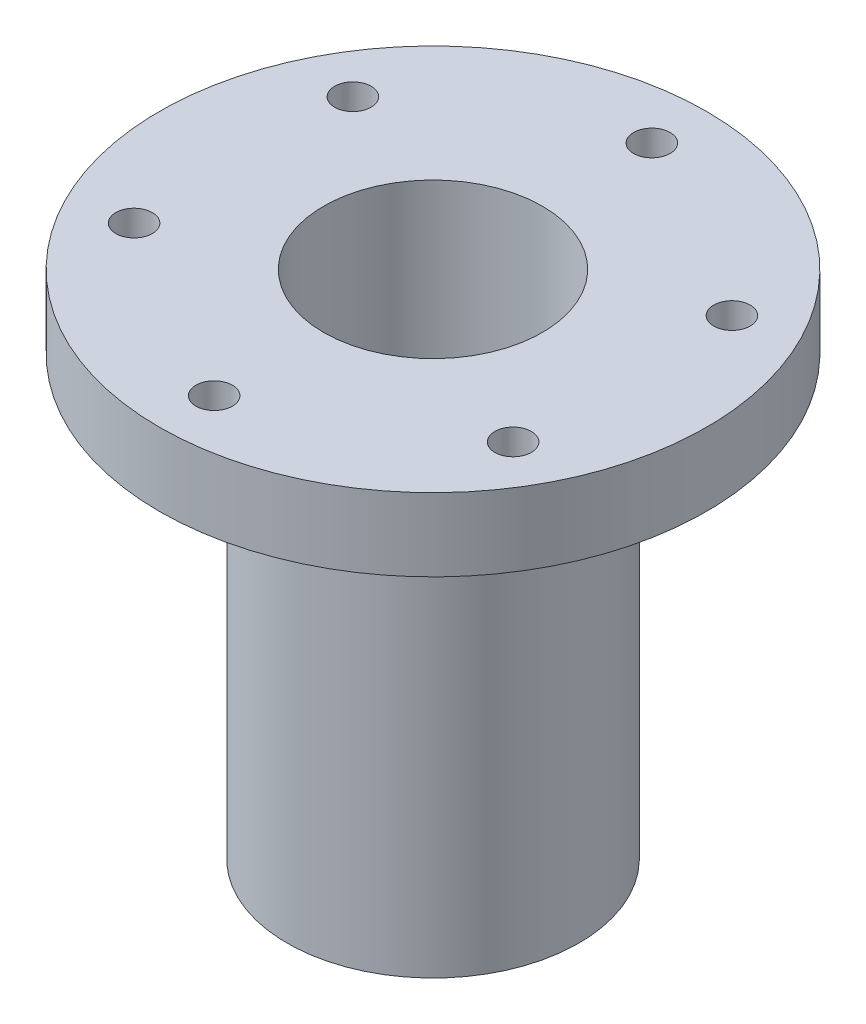
SolidWorks part; units mm, degrees
ref_plane "Front Plane" through (0, 0, 0) normal (0, 0, 1) x (1, 0, 0)
ref_plane "Top Plane" through (0, 0, 0) normal (0, 1, 0) x (1, 0, 0)
ref_plane "Right Plane" through (0, 0, 0) normal (1, 0, 0) x (0, 0, -1)
sketch "Sketch1" plane through (0, 0, 0) normal (0, 0, 1) x (1, 0, 0)
  line L0 (-9.525, -31.1997) -> (-9.525, 13.2503)
  line L1 (-9.525, 13.2503) -> (-23.8125, 13.2503)
  line L2 (-23.8125, 13.2503) -> (-23.8125, 6.9003)
  line L3 (-23.8125, 6.9003) -> (-12.7, 6.9003)
  line L4 (-12.7, 6.9003) -> (-12.7, -31.1997)
  line L5 (-12.7, -31.1997) -> (-9.525, -31.1997)
  line L6 (0, 0) -> (0, 31.9657) construction
  dimension "D1" = 3.175
  dimension "D2" = 6.35
  dimension "D3" = 12.7
  dimension "D4" = 23.8125
  dimension "D5" = 38.1
revolve "Revolve1" add sketch "Sketch1" angle 360 about L6
hole_wizard "1/8 (0.125) Diameter Hole2" positions "Sketch2" profile "Sketch3" hole size "1/8" standard "ANSI Inch" end condition through all
sketch "Sketch2" plane through (0, 6.9003, 0) normal (0, -1, 0) x (-1, 0, 0)
  line L0 (0, 0) -> (0, 23.8125) construction
  circle A0 centre (0, 0) radius 23.8125 construction
  point P0 (0, 19.05)
  point P14 (16.4978, 9.525)
  point P15 (16.4978, -9.525)
  point P16 (0, -19.05)
  point P17 (-16.4978, -9.525)
  point P18 (-16.4978, 9.525)
  point P19 (0, 0)
  dimension "D1" = 19.05
  dimension "D2" = 6
sketch "Sketch3" plane through (0, 6.9003, -19.05) normal (1, 0, 0) x (0, 0, -1)
  line L0 (0, 0) -> (0, 6.35)
  line L1 (0, 6.35) -> (1.5875, 6.35)
  line L2 (1.5875, 6.35) -> (1.5875, 0)
  line L5 (1.5875, 0) -> (0, 0)
  line L11 (0, -6.35) -> (0, 107.95) construction
  dimension "Thru Hole Dia." = 3.175
  dimension "Thru Hole Depth" = 6.35
